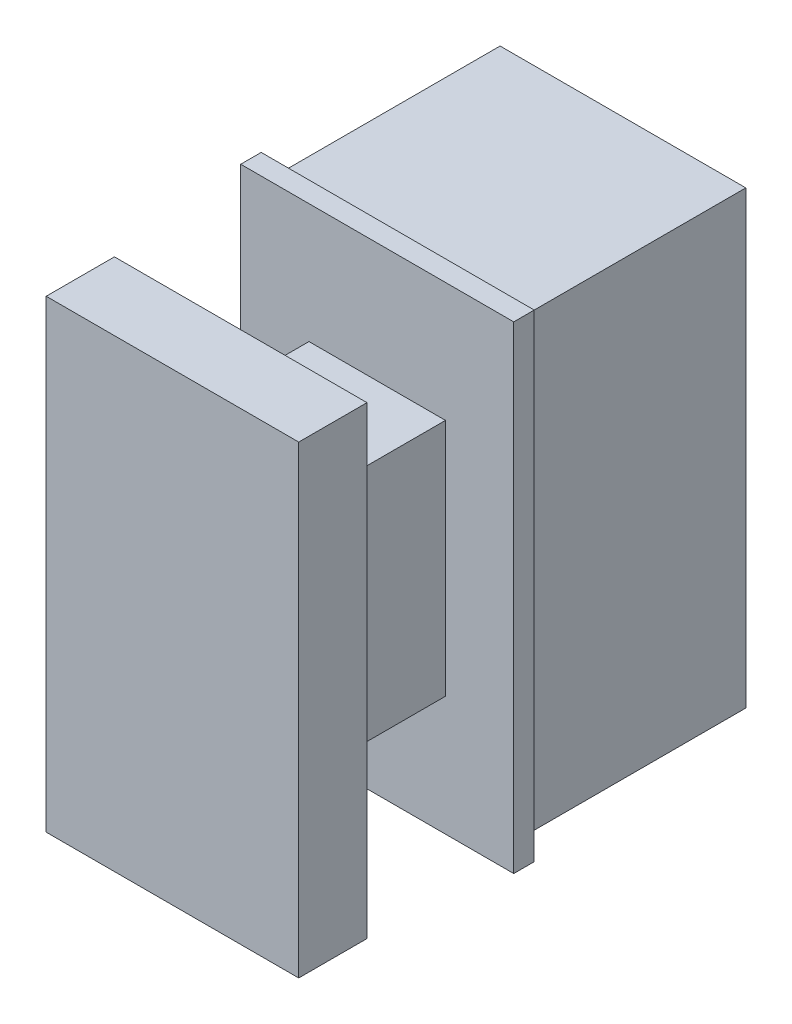
SolidWorks part; units mm, degrees
ref_plane "Piano frontale" through (0, 0, 0) normal (0, 0, 1) x (1, 0, 0)
ref_plane "Piano superiore" through (0, 0, 0) normal (0, 1, 0) x (1, 0, 0)
ref_plane "Piano destro" through (0, 0, 0) normal (1, 0, 0) x (0, 0, -1)
sketch "Schizzo1" plane through (0, 0, 0) normal (0, 0, 1) x (1, 0, 0)
  line L5 (0, 0) -> (4, 0)
  line L6 (0, 0) -> (0, 7)
  line L7 (0, 7) -> (4, 7)
  line L8 (4, 0) -> (4, 7)
  dimension "D1" = 4
  dimension "D2" = 7
extrude "Estrusione-Estrusione1" add sketch "Schizzo1" along normal blind 0.3
sketch "Schizzo2" plane through (0, 0, 0) normal (0, 0, 1) x (1, 0, 0)
  line L0 (0, 0) -> (4, 0) construction
  line L1 (0.2, 6.8) -> (3.8, 6.8)
  line L2 (0.2, 6.8) -> (0.2, 0.2)
  line L3 (0.2, 0.2) -> (3.8, 0.2)
  line L4 (3.8, 6.8) -> (3.8, 0.2)
  line L5 (4, 0) -> (4, 7) construction
  line L6 (4, 7) -> (0, 7) construction
  line L7 (0, 7) -> (0, 0) construction
  line L8 (0, 0) -> (4, 0)
  line L9 (4, 0) -> (4, 7)
  line L10 (4, 7) -> (0, 7)
  line L11 (0, 7) -> (0, 0)
  dimension "D1" = 0.2
  dimension "D2" = 0.2
  dimension "D3" = 0.2
  dimension "D4" = 0.2
extrude "Estrusione-Estrusione2" add sketch "Schizzo2" against normal blind 3.3 contours L2 L1 L4 L3
sketch "Schizzo3" plane through (0, 0, 0) normal (0, 0, 1) x (1, 0, 0)
  line L0 (0.2, 6.8) -> (3.8, 6.8) construction
  line L1 (3.6, 6.6) -> (0.4, 6.6)
  line L2 (3.6, 6.6) -> (3.6, 0.4)
  line L3 (3.6, 0.4) -> (0.4, 0.4)
  line L4 (0.4, 6.6) -> (0.4, 0.4)
  line L5 (0.2, 0.2) -> (3.8, 0.2) construction
  line L6 (3.8, 6.8) -> (3.8, 0.2) construction
  line L7 (0.2, 6.8) -> (0.2, 0.2) construction
  dimension "D1" = 0.2
  dimension "D2" = 0.2
  dimension "D3" = 0.2
  dimension "D4" = 0.2
extrude "Taglio-Estrusione1" cut sketch "Schizzo3" against normal through all
sketch "Schizzo6" plane through (0, 0, 0) normal (0, 0, 1) x (1, 0, 0)
  line L0 (4, 3.5) -> (0, 3.5) construction
  line L1 (4, 0) -> (4, 7) construction
  line L2 (0, 7) -> (0, 0) construction
  line L3 (0, 3.5) -> (2, 3.5) construction
  line L4 (2, 3.5) -> (2, 0) construction
  line L5 (0, 0) -> (4, 0) construction
  line L6 (2, 3.5) -> (2, 7) construction
  line L7 (4, 7) -> (0, 7) construction
  line L13 (1, 1.75) -> (3, 1.75)
  line L14 (1, 1.75) -> (1, 5.25)
  line L15 (1, 5.25) -> (3, 5.25)
  line L16 (3, 1.75) -> (3, 5.25)
  line L17 (1, 1.75) -> (3, 5.25) construction
  line L18 (1, 5.25) -> (3, 1.75) construction
  dimension "D1" = 2
  dimension "D2" = 3.5
extrude "Estrusione-Estrusione3" add sketch "Schizzo6" along normal blind 2.3 contours L14 L13 L16 L15
sketch "Schizzo7" plane through (0, 0, 2.3) normal (0, 0, 1) x (1, 0, 0)
  line L0 (1, 5.25) -> (2, 5.25) construction
  line L1 (1, 5.25) -> (3, 5.25) construction
  line L2 (2, 5.25) -> (2, 1.75) construction
  line L3 (1, 1.75) -> (3, 1.75) construction
  line L4 (2, 1.75) -> (3, 1.75) construction
  line L5 (3, 1.75) -> (1, 5.25) construction
  line L6 (1, 5.25) -> (1, 1.75) construction
  line L7 (1, 1.75) -> (3, 5.25) construction
  line L9 (0.15, 6.9) -> (3.85, 6.9)
  line L10 (0.15, 6.9) -> (0.15, 0.1)
  line L11 (0.15, 0.1) -> (3.85, 0.1)
  line L12 (3.85, 6.9) -> (3.85, 0.1)
  line L13 (0.15, 6.9) -> (3.85, 0.1) construction
  line L14 (0.15, 0.1) -> (3.85, 6.9) construction
  point P13 (2, 3.5)
  dimension "D1" = 3.7
  dimension "D2" = 6.8
extrude "Estrusione-Estrusione4" add sketch "Schizzo7" along normal blind 1
